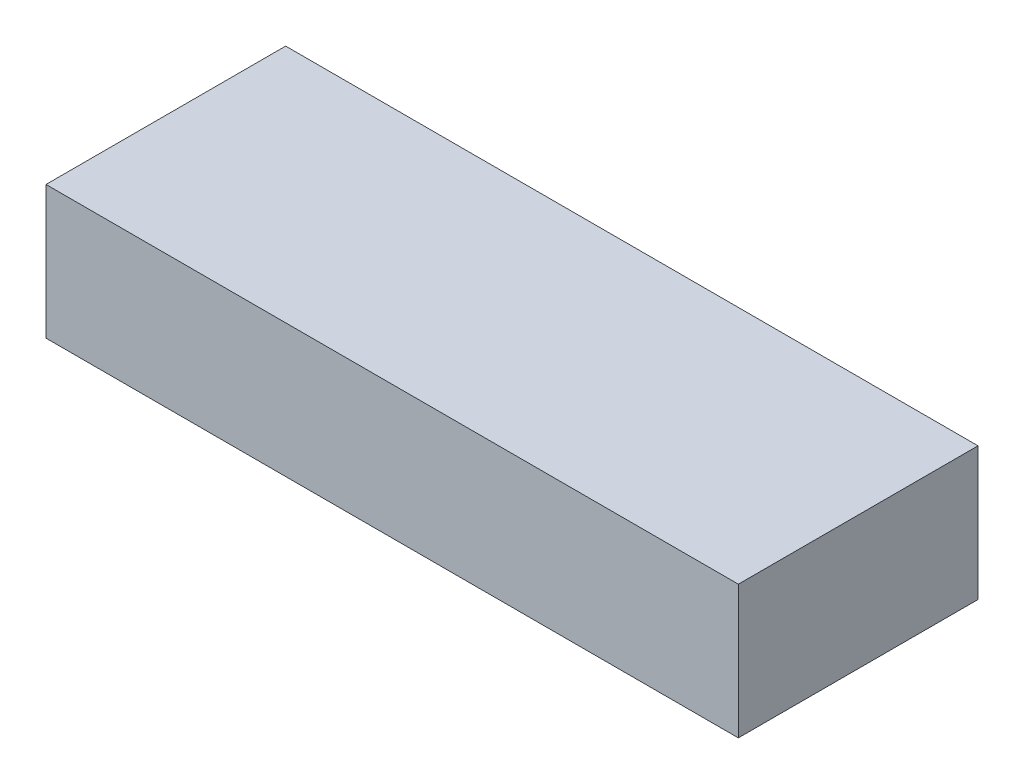
SolidWorks part; units mm, degrees
material "PVC 0.007 plastifié"
ref_plane "Face" through (0, 0, 0) normal (0, 0, 1) x (1, 0, 0)
ref_plane "Dessus" through (0, 0, 0) normal (0, 1, 0) x (1, 0, 0)
ref_plane "Droite" through (0, 0, 0) normal (1, 0, 0) x (0, 0, -1)
sketch "Esquisse1" plane through (0, 0, 0) normal (0, 0, 1) x (1, 0, 0)
  line L0 (0, 0) -> (0, 20.6952) construction
  line L1 (-13, -2.5) -> (13, -2.5)
  line L2 (-13, -2.5) -> (-13, 2.5)
  line L3 (-13, 2.5) -> (13, 2.5)
  line L4 (13, -2.5) -> (13, 2.5)
  line L5 (0, 0) -> (20.3908, 0) construction
  dimension "D1" = 26
  dimension "D2" = 5
extrude "Extrusion1" add sketch "Esquisse1" along normal blind 9
